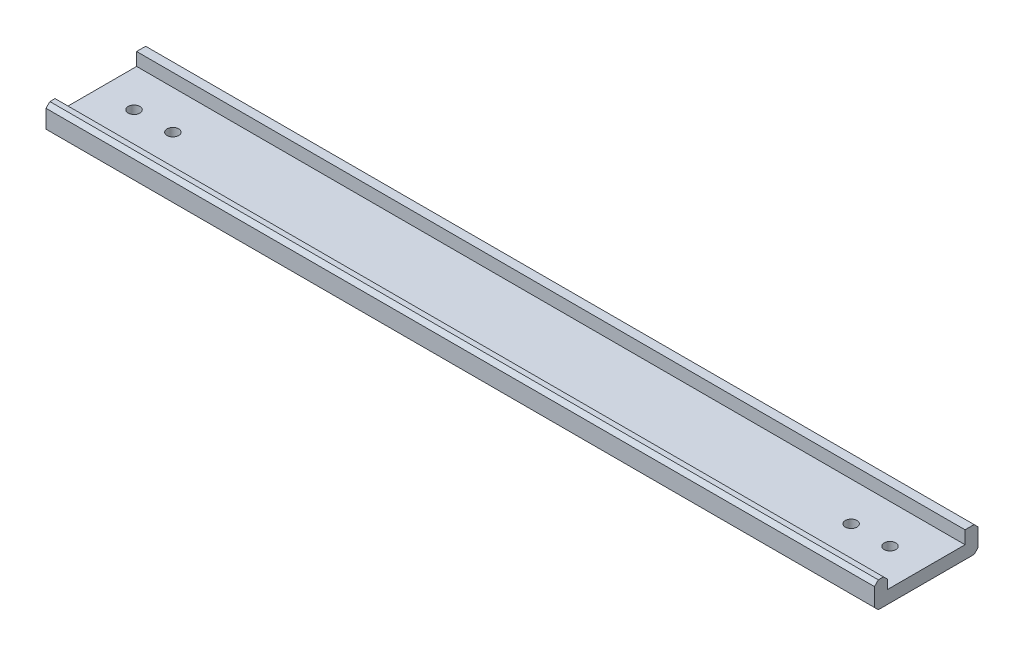
SolidWorks part; units mm, degrees
material "ABS"
ref_plane "Alzado" through (0, 0, 0) normal (0, 0, 1) x (1, 0, 0)
ref_plane "Planta" through (0, 0, 0) normal (0, 1, 0) x (1, 0, 0)
ref_plane "Vista lateral" through (0, 0, 0) normal (1, 0, 0) x (0, 0, -1)
sketch "Croquis1" plane through (0, 0, 0) normal (1, 0, 0) x (0, 0, -1)
  line L0 (-15, 0) -> (15, 0)
  line L1 (-15, 0) -> (-15, 5)
  line L2 (-15, 5) -> (-20, 5)
  line L3 (-20, 5) -> (-20, -5)
  line L4 (-20, -5) -> (20, -5)
  line L5 (20, -5) -> (20, 5)
  line L6 (20, 5) -> (15, 5)
  line L7 (15, 5) -> (15, 0)
  point P4 (0, 0)
  dimension "D1" = 5
  dimension "D2" = 5
  dimension "D3" = 30
  dimension "D4" = 5
extrude "Saliente-Extruir1" add sketch "Croquis1" along normal mid plane 320
chamfer "Chaflán1" distance 1.5 angle 45 5 edges at (0, 5, 15) (0, 5, -20) (0, 5, 20) (0, -5, -20) (0, -5, 20)
sketch "Croquis2" plane through (0, 0, 0) normal (0, 1, 0) x (1, 0, 0)
  line L0 (-146, 0) -> (-131, 0) construction
  line L1 (-131, 0) -> (131, 0) construction
  line L2 (131, 0) -> (146, 0) construction
  circle A0 centre (-146, 0) radius 2.25
  circle A1 centre (-131, 0) radius 2.25
  circle A2 centre (131, 0) radius 2.25
  circle A3 centre (146, 0) radius 2.25
  point P8 (0, 0)
  dimension "D3" = 4.5
  dimension "D1" = 262
  dimension "D2" = 15
extrude "Cortar-Extruir1" cut sketch "Croquis2" against normal blind 320
